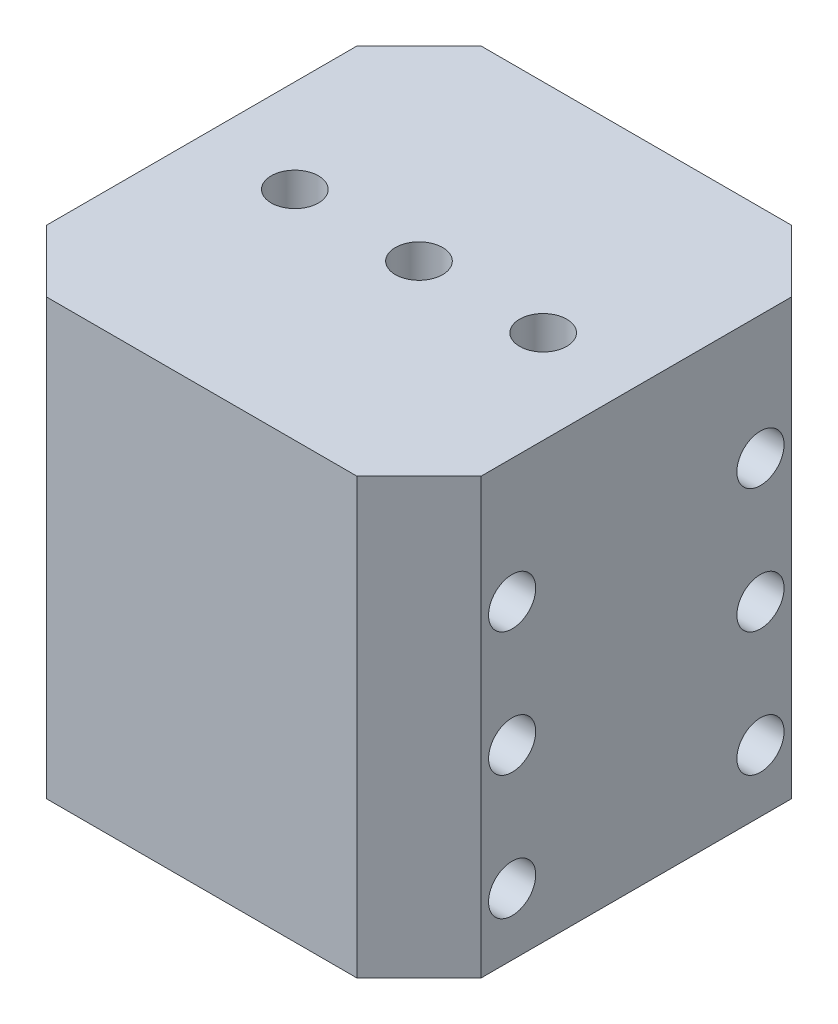
SolidWorks part; units mm, degrees
ref_plane "Front Plane" through (0, 0, 0) normal (0, 0, 1) x (1, 0, 0)
ref_plane "Top Plane" through (0, 0, 0) normal (0, 1, 0) x (1, 0, 0)
ref_plane "Right Plane" through (0, 0, 0) normal (1, 0, 0) x (0, 0, -1)
sketch "Sketch1" plane through (0, 0, 0) normal (0, 1, 0) x (1, 0, 0)
  line L0 (0, 38.1) -> (6.35, 44.45)
  line L1 (6.35, 0) -> (38.1, 0)
  line L2 (0, 6.35) -> (0, 38.1)
  line L3 (6.35, 44.45) -> (38.1, 44.45)
  line L4 (44.45, 6.35) -> (44.45, 38.1)
  line L5 (0, 6.35) -> (6.35, 0)
  line L6 (38.1, 0) -> (44.45, 6.35)
  line L7 (38.1, 44.45) -> (44.45, 38.1)
  line L9 (-3.175, 47.625) -> (47.625, 47.625) construction
  line L10 (-3.175, 47.625) -> (-3.175, -3.175) construction
  line L11 (-3.175, -3.175) -> (47.625, -3.175) construction
  line L12 (47.625, 47.625) -> (47.625, -3.175) construction
  circle A0 centre (9.525, 22.225) radius 2.413
  circle A1 centre (22.225, 22.225) radius 2.413
  circle A2 centre (34.925, 22.225) radius 2.413
  point P0 (0, 0)
  point P1 (44.45, 44.45)
  point P2 (0, 44.45)
  point P3 (44.45, 0)
  point P23 (47.625, 22.225)
  point P24 (0, 22.225)
  point P25 (22.225, 44.45)
  point P26 (22.225, 47.625)
  point P29 (18.4045, 29.4266)
  dimension "D3" = 4.826
  dimension "D1" = 44.45
  dimension "D2" = 44.45
  dimension "D4" = 50.8
  dimension "D5" = 25.4
  dimension "D6" = 12.7
  dimension "D7" = 12.7
extrude "Boss-Extrude1" add sketch "Sketch1" along normal blind 44.45
sketch "Sketch2" plane through (44.45, 0, 0) normal (1, 0, 0) x (0, 0, -1)
  line L0 (6.35, 0) -> (38.1, 0) construction
  line L1 (-3.175, 47.625) -> (47.625, 47.625) construction
  line L2 (-3.175, 47.625) -> (-3.175, -3.175) construction
  line L3 (-3.175, -3.175) -> (47.625, -3.175) construction
  line L4 (47.625, 47.625) -> (47.625, -3.175) construction
  line L5 (0, 44.45) -> (0, 0) construction
  line L6 (6.35, 44.45) -> (38.1, 44.45) construction
  circle A0 centre (9.525, 31.75) radius 2.413
  circle A1 centre (34.925, 31.75) radius 2.413
  circle A2 centre (34.925, 6.35) radius 2.413
  circle A3 centre (9.525, 6.35) radius 2.413
  circle A4 centre (9.525, 19.05) radius 2.413
  circle A5 centre (34.925, 19.05) radius 2.413
  point P11 (22.225, 0)
  point P16 (22.225, 47.625)
  point P19 (0, 22.225)
  point P20 (-3.175, 22.225)
  point P26 (0, 0)
  point P27 (0, 0)
  point P28 (0, 0)
  dimension "D1" = 4.826
  dimension "D2" = 50.8
  dimension "D3" = 12.7
  dimension "D4" = 12.7
  dimension "D5" = 12.7
  dimension "D6" = 25.4
  dimension "D7" = 12.7
extrude "Cut-Extrude1" cut sketch "Sketch2" against normal blind 50.8
